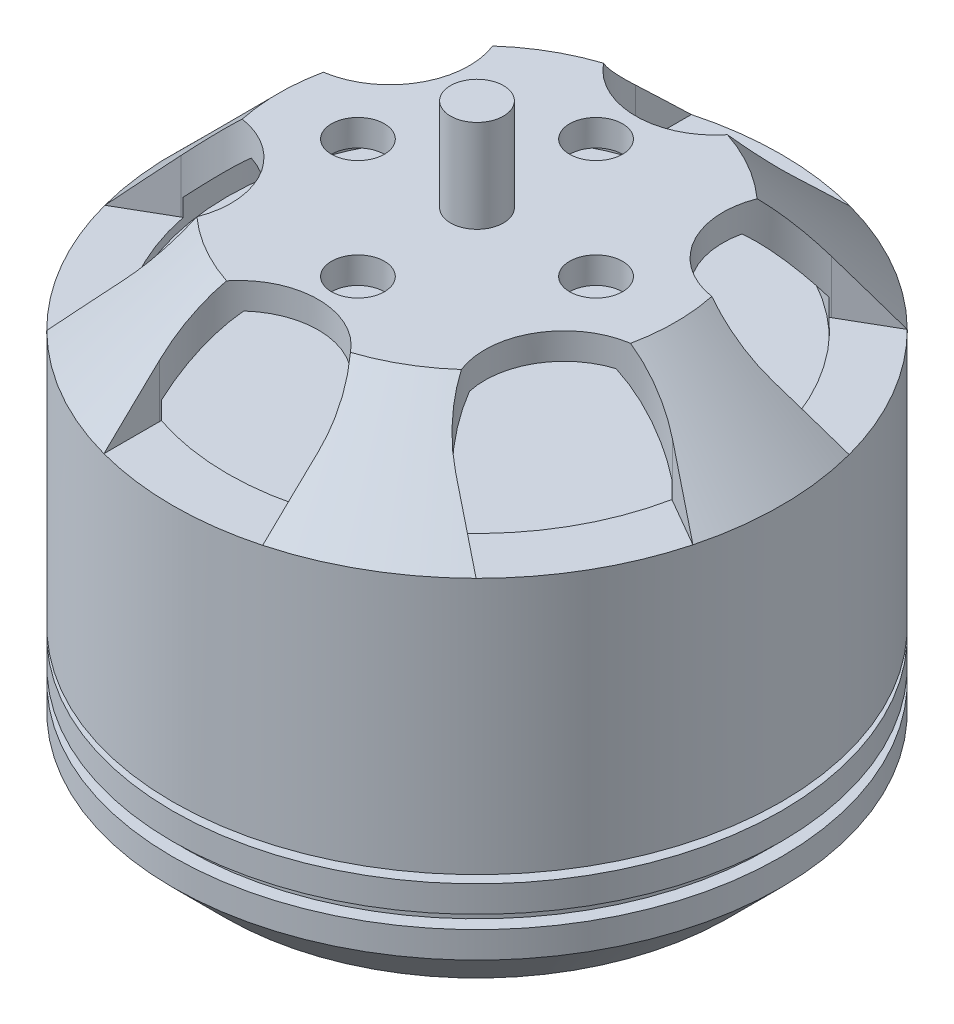
SolidWorks part; units mm, degrees
ref_plane "Front Plane" through (0, 0, 0) normal (0, 0, 1) x (1, 0, 0)
ref_plane "Top Plane" through (0, 0, 0) normal (0, 1, 0) x (1, 0, 0)
ref_plane "Right Plane" through (0, 0, 0) normal (1, 0, 0) x (0, 0, -1)
sketch "Sketch1" plane through (0, 0, 0) normal (0, 0, 1) x (1, 0, 0)
  line L0 (0, 20.602) -> (0, 0)
  line L1 (1, -1.398) -> (9.5, -1.398)
  line L2 (9.5, -1.398) -> (11.5, 0.602)
  line L3 (11.5, 0.602) -> (11.5, 1.602)
  line L4 (11.5, 13.102) -> (7.5, 17.102)
  line L5 (7.5, 17.102) -> (1, 17.102)
  line L6 (1, 17.102) -> (1, 20.602)
  line L7 (1, 20.602) -> (0, 20.602)
  line L8 (0, 0) -> (0, -3.198)
  line L9 (0, -3.198) -> (1, -3.198)
  line L10 (1, -3.198) -> (1, -1.398)
  line L11 (2, 16.102) -> (7.0858, 16.102)
  line L12 (7.0858, 16.102) -> (9.423, 13.7647)
  line L13 (9.423, 13.7647) -> (9.423, 12.7647)
  line L14 (9.423, 12.7647) -> (1, 12.7647)
  line L15 (1, 12.7647) -> (1, 15.102)
  line L16 (1, 15.102) -> (2, 15.102)
  line L17 (2, 15.102) -> (2, 16.102)
  line L18 (11.5, 1.602) -> (11, 1.602)
  line L19 (11, 1.602) -> (11, 2.102)
  line L20 (11, 2.102) -> (11.5, 2.102)
  line L21 (11.5, 3.102) -> (9.5, 3.102)
  line L22 (9.5, 3.102) -> (9.5, 3.402)
  line L23 (9.5, 3.402) -> (11.5, 3.402)
  line L24 (11.5, 2.102) -> (11.5, 3.102)
  line L25 (11.5, 3.402) -> (11.5, 13.102)
  dimension "D1" = 23.8
  dimension "D2" = 1.8
  dimension "D3" = 45
  dimension "D4" = 2
  dimension "D5" = 11.5
  dimension "D6" = 1
  dimension "D7" = 1
  dimension "D8" = 3.5
  dimension "D9" = 1
  dimension "D10" = 1
  dimension "D11" = 1
  dimension "D12" = 1
  dimension "D13" = 1
  dimension "D14" = 1
  dimension "D15" = 45
  dimension "D16" = 4
  dimension "D17" = 0.5
  dimension "D18" = 0.5
  dimension "D19" = 1
  dimension "D20" = 2
  dimension "D21" = 0.3
  dimension "D22" = 1
revolve "Revolve1" add sketch "Sketch1" angle 360 about L0
sketch "Sketch2" plane through (0, 17.102, 0) normal (0, 1, 0) x (1, 0, 0)
  line L0 (0, 0) -> (0, 9) construction
  line L1 (-3, 9) -> (-3, 16.7794)
  line L2 (-3, 16.7794) -> (3, 16.7794)
  line L3 (3, 16.7794) -> (3, 9)
  line L4 (6.2942, 7.0981) -> (13.0314, 10.9878)
  line L5 (16.0314, 5.7916) -> (9.2942, 1.9019)
  line L6 (13.0314, 10.9878) -> (16.0314, 5.7916)
  line L7 (9.2942, -1.9019) -> (16.0314, -5.7916)
  line L8 (13.0314, -10.9878) -> (6.2942, -7.0981)
  line L9 (16.0314, -5.7916) -> (13.0314, -10.9878)
  line L10 (3, -9) -> (3, -16.7794)
  line L11 (-3, -16.7794) -> (-3, -9)
  line L12 (3, -16.7794) -> (-3, -16.7794)
  line L13 (-6.2942, -7.0981) -> (-13.0314, -10.9878)
  line L14 (-16.0314, -5.7916) -> (-9.2942, -1.9019)
  line L15 (-13.0314, -10.9878) -> (-16.0314, -5.7916)
  line L16 (-9.2942, 1.9019) -> (-16.0314, 5.7916)
  line L17 (-13.0314, 10.9878) -> (-6.2942, 7.0981)
  line L18 (-16.0314, 5.7916) -> (-13.0314, 10.9878)
  circle A0 centre (0, 0) radius 4.5 construction
  circle A1 centre (0, 0) radius 9.2211 construction
  circle A2 centre (0, -4.5) radius 1
  circle A3 centre (-4.5, 0) radius 1
  circle A4 centre (0, 4.5) radius 1
  circle A5 centre (4.5, 0) radius 1
  arc A6 (-3, 9) -> (3, 9) centre (0, 9) ccw
  arc A7 (6.2942, 7.0981) -> (9.2942, 1.9019) centre (7.7942, 4.5) ccw
  arc A8 (9.2942, -1.9019) -> (6.2942, -7.0981) centre (7.7942, -4.5) ccw
  arc A9 (3, -9) -> (-3, -9) centre (0, -9) ccw
  arc A10 (-6.2942, -7.0981) -> (-9.2942, -1.9019) centre (-7.7942, -4.5) ccw
  arc A11 (-9.2942, 1.9019) -> (-6.2942, 7.0981) centre (-7.7942, 4.5) ccw
  dimension "D1" = 9
  dimension "D3" = 2
  dimension "D5" = 6
  dimension "D2" = 9
  dimension "D4" = 4
  dimension "D6" = 6
extrude "Cut-Extrude1" cut sketch "Sketch2" against normal blind 4
sketch "Sketch3" plane through (0, -1.398, 0) normal (0, -1, 0) x (1, 0, 0)
  circle A0 centre (0, 0) radius 6 construction
  circle A1 centre (0, 0) radius 8 construction
  circle A2 centre (0, 6) radius 1
  circle A3 centre (0, -6) radius 1
  circle A4 centre (-8, 0) radius 1
  circle A5 centre (8, 0) radius 1
  dimension "D1" = 12
  dimension "D2" = 16
  dimension "D3" = 2
extrude "Cut-Extrude2" cut sketch "Sketch3" against normal blind 3
